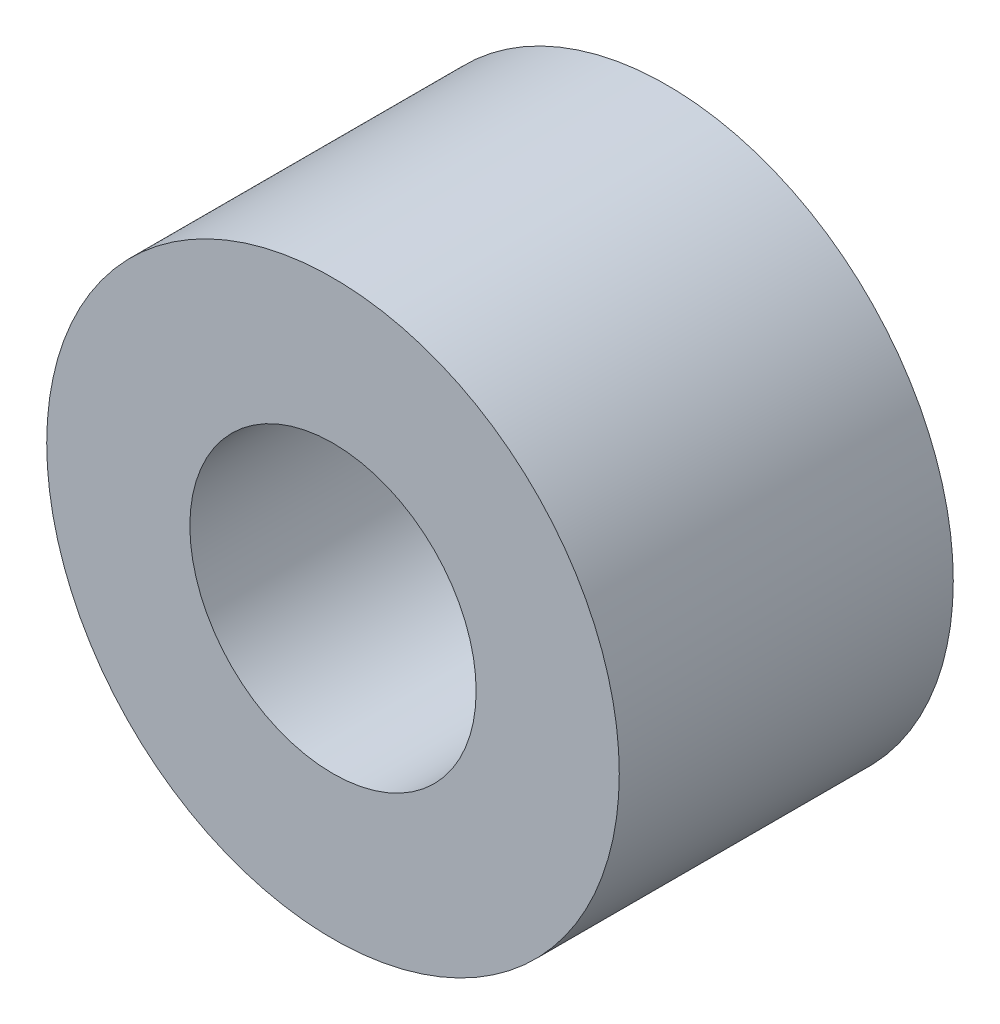
SolidWorks part; units mm, degrees
ref_plane "正面" through (0, 0, 0) normal (0, 0, 1) x (1, 0, 0)
ref_plane "平面" through (0, 0, 0) normal (0, 1, 0) x (1, 0, 0)
ref_plane "右側面" through (0, 0, 0) normal (1, 0, 0) x (0, 0, -1)
sketch "ｽｹｯﾁ1" plane through (0, 0, 0) normal (0, 0, 1) x (1, 0, 0)
  circle A0 centre (8, 30) radius 3
  circle A1 centre (8, 30) radius 6
  dimension "D1" = 3
extrude "ﾎﾞｽ - 押し出し1" add sketch "ｽｹｯﾁ1" along normal blind 7 from surface at 3
